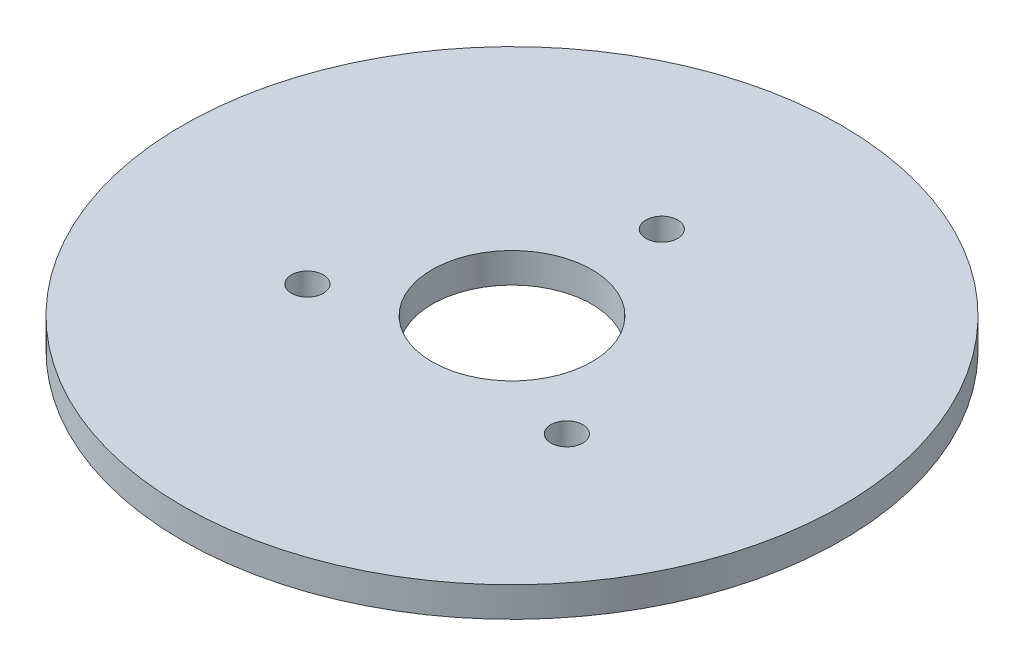
SolidWorks part; units mm, degrees
material "Carbon Fiber"
ref_plane "Front Plane" through (0, 0, 0) normal (0, 0, 1) x (1, 0, 0)
ref_plane "Top Plane" through (0, 0, 0) normal (0, 1, 0) x (1, 0, 0)
ref_plane "Right Plane" through (0, 0, 0) normal (1, 0, 0) x (0, 0, -1)
sketch "Sketch1" plane through (0, 0, 0) normal (0, 1, 0) x (1, 0, 0)
  line L0 (0, 0) -> (0, 15) construction
  circle A0 centre (0, 0) radius 33
  circle A1 centre (0, 15) radius 1.6
  circle A2 centre (12.9904, -7.5) radius 1.6
  circle A3 centre (-12.9904, -7.5) radius 1.6
  circle A4 centre (0, 0) radius 8
  point P12 (0, 0)
  dimension "D1" = 66
  dimension "D3" = 3.2
  dimension "D5" = 16
  dimension "D2" = 15
  dimension "D4" = 3
extrude "Boss-Extrude1" add sketch "Sketch1" along normal blind 3
